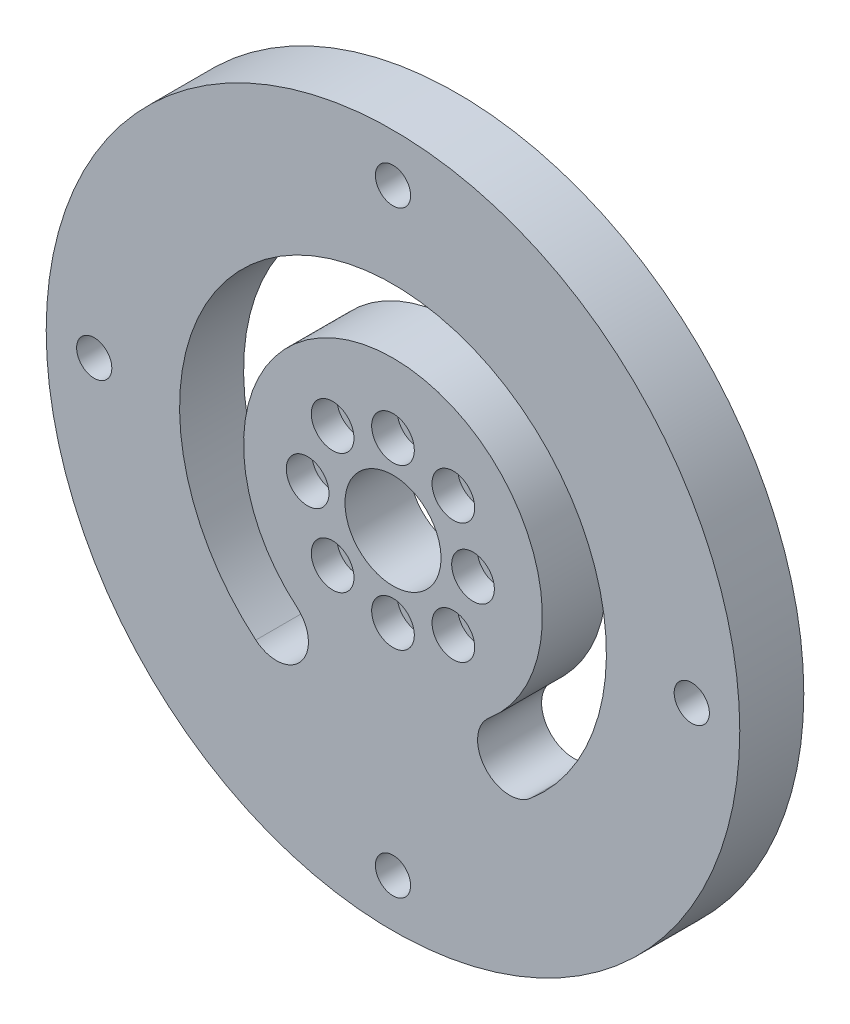
SolidWorks part; units mm, degrees
ref_plane "Front Plane" through (0, 0, 0) normal (0, 0, 1) x (1, 0, 0)
ref_plane "Top Plane" through (0, 0, 0) normal (0, 1, 0) x (1, 0, 0)
ref_plane "Right Plane" through (0, 0, 0) normal (1, 0, 0) x (0, 0, -1)
sketch "Sketch1" plane through (0, 0, 0) normal (0, 0, 1) x (1, 0, 0)
  circle A0 centre (0, 0) radius 32.5
  dimension "D1" = 65
extrude "Boss-Extrude1" add sketch "Sketch1" along normal blind 6
sketch "Sketch16" plane through (0, 0, 6) normal (0, 0, 1) x (1, 0, 0)
  line L0 (-8, 0) -> (0, 0) construction
  circle A1 centre (-8, 0) radius 1
  circle A4 centre (-5.6569, 5.6569) radius 1
  circle A5 centre (0, 8) radius 1
  circle A6 centre (5.6569, 5.6569) radius 1
  circle A7 centre (8, 0) radius 1
  circle A8 centre (5.6569, -5.6569) radius 1
  circle A9 centre (0, -8) radius 1
  circle A10 centre (-5.6569, -5.6569) radius 1
  point P22 (0, 0)
  dimension "D1" = 8
  dimension "D2" = 2
  dimension "D3" = 8
extrude "Cut-Extrude8" cut sketch "Sketch16" against normal through all
sketch "Sketch17" plane through (0, 0, 6) normal (0, 0, 1) x (1, 0, 0)
  circle A0 centre (7.5, 0) radius 2
  circle A1 centre (-8, 0) radius 2
  circle A2 centre (0, -7.5) radius 2
  circle A3 centre (0, 7.5) radius 2
  circle A4 centre (-5.6569, 5.6569) radius 2
  circle A5 centre (5.6569, 5.6569) radius 2
  circle A6 centre (5.6569, -5.6569) radius 2
  circle A7 centre (-5.6569, -5.6569) radius 2
  dimension "D1" = 4
extrude "Cut-Extrude9" cut sketch "Sketch17" against normal blind 2.4
sketch "Sketch18" plane through (0, 0, 0) normal (0, 0, -1) x (-1, 0, 0)
  circle A0 centre (0, 0) radius 4.5
  dimension "D1" = 9
extrude "Cut-Extrude10" cut sketch "Sketch18" against normal through all
sketch "Sketch19" plane through (0, 0, 6) normal (0, 0, 1) x (1, 0, 0)
  line L0 (0, 28) -> (0, 0) construction
  circle A0 centre (0, 28) radius 1.65
  circle A1 centre (28, 0) radius 1.65
  circle A2 centre (0, -28) radius 1.65
  circle A3 centre (-28, 0) radius 1.65
  point P13 (0, 0)
  dimension "D2" = 3.3
  dimension "D1" = 28
  dimension "D3" = 4
extrude "Cut-Extrude11" cut sketch "Sketch19" against normal blind 10
sketch "Sketch20" plane through (0, 0, 0) normal (0, 0, -1) x (-1, 0, 0)
  line L1 (1.6166, 30.8) -> (-1.6166, 30.8)
  line L2 (-1.6166, 30.8) -> (-3.2332, 28)
  line L3 (-3.2332, 28) -> (-1.6166, 25.2)
  line L4 (-1.6166, 25.2) -> (1.6166, 25.2)
  line L5 (1.6166, 25.2) -> (3.2332, 28)
  line L6 (3.2332, 28) -> (1.6166, 30.8)
  line L7 (29.6166, 2.8) -> (26.3834, 2.8)
  line L8 (26.3834, 2.8) -> (24.7668, 0)
  line L9 (24.7668, 0) -> (26.3834, -2.8)
  line L10 (26.3834, -2.8) -> (29.6166, -2.8)
  line L11 (29.6166, -2.8) -> (31.2332, 0)
  line L12 (31.2332, 0) -> (29.6166, 2.8)
  line L13 (1.6166, -25.2) -> (-1.6166, -25.2)
  line L14 (-1.6166, -25.2) -> (-3.2332, -28)
  line L15 (-3.2332, -28) -> (-1.6166, -30.8)
  line L16 (-1.6166, -30.8) -> (1.6166, -30.8)
  line L17 (1.6166, -30.8) -> (3.2332, -28)
  line L18 (3.2332, -28) -> (1.6166, -25.2)
  line L19 (-26.3834, 2.8) -> (-29.6166, 2.8)
  line L20 (-29.6166, 2.8) -> (-31.2332, 0)
  line L21 (-31.2332, 0) -> (-29.6166, -2.8)
  line L22 (-29.6166, -2.8) -> (-26.3834, -2.8)
  line L23 (-26.3834, -2.8) -> (-24.7668, 0)
  line L24 (-24.7668, 0) -> (-26.3834, 2.8)
  circle A0 centre (0, 28) radius 2.8 construction
  circle A1 centre (28, 0) radius 2.8 construction
  circle A2 centre (0, -28) radius 2.8 construction
  circle A3 centre (-28, 0) radius 2.8 construction
  dimension "D1" = 5.6
extrude "Cut-Extrude12" cut sketch "Sketch20" against normal blind 3
sketch "Sketch21" plane through (0, 0, 6) normal (0, 0, 1) x (1, 0, 0)
  line L0 (0, 0) -> (0, -18.8551) construction
  line L1 (0, 0) -> (12.8558, -15.3209) construction
  line L2 (0, 0) -> (-12.8558, -15.3209) construction
  arc A0 (12.8558, -15.3209) -> (-12.8558, -15.3209) centre (0, 0) ccw
  arc A1 (8.999, -10.7246) -> (-8.999, -10.7246) centre (0, 0) ccw
  arc A2 (-12.8558, -15.3209) -> (-8.999, -10.7246) centre (-10.9274, -13.0228) ccw
  arc A3 (8.999, -10.7246) -> (12.8558, -15.3209) centre (10.9274, -13.0228) ccw
  dimension "D3" = 14
  dimension "D1" = 6
  dimension "D2" = 40
extrude "Cut-Extrude13" cut sketch "Sketch21" against normal through all
